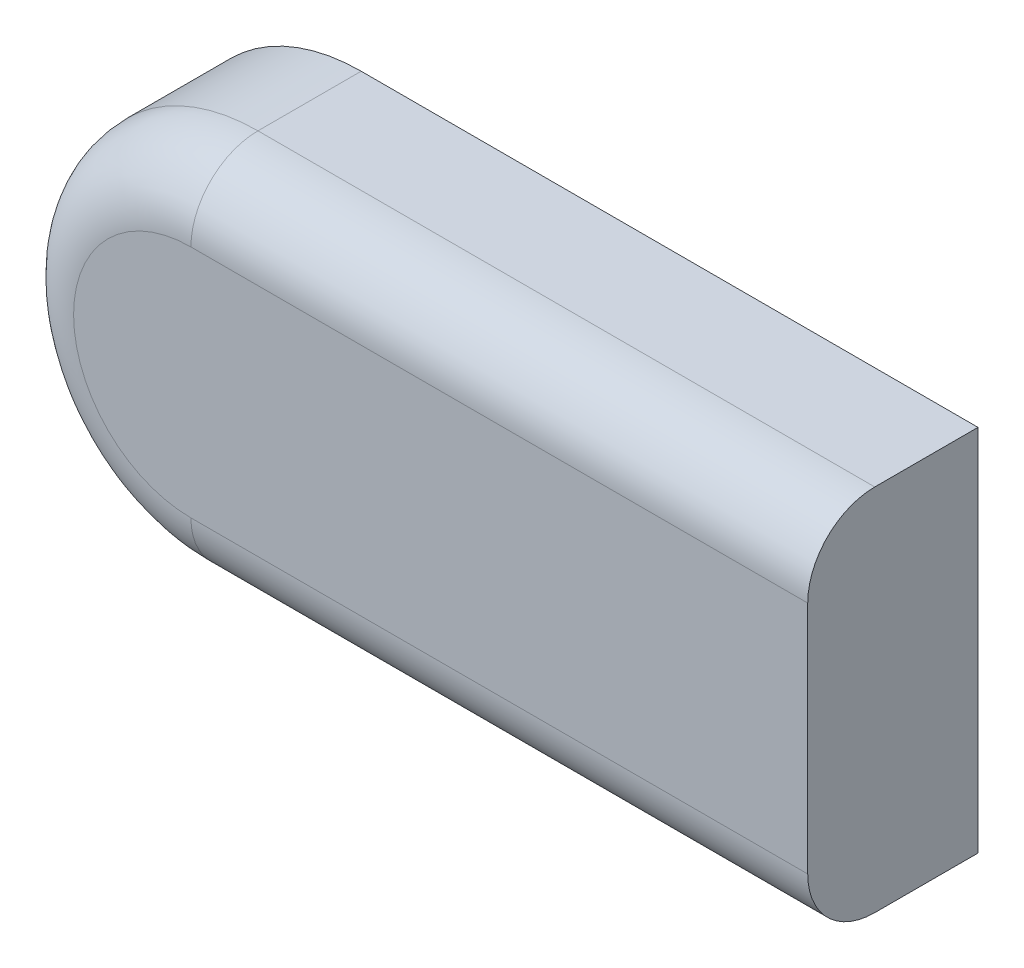
SolidWorks part; units mm, degrees
ref_plane "Front Plane" through (0, 0, 0) normal (0, 0, 1) x (1, 0, 0)
ref_plane "Top Plane" through (0, 0, 0) normal (0, 1, 0) x (1, 0, 0)
ref_plane "Right Plane" through (0, 0, 0) normal (1, 0, 0) x (0, 0, -1)
sketch "Sketch4" plane through (0, 0, 0) normal (0, 0, 1) x (1, 0, 0)
  line L1 (79.1182, 41.2761) -> (-12.8937, 41.2761)
  line L2 (79.1182, 41.2761) -> (79.1182, -13.7239)
  line L3 (79.1182, -13.7239) -> (-12.8937, -13.7239)
  line L5 (-12.4727, 38.2761) -> (76.1182, 38.2761)
  line L7 (-12.4727, -10.7239) -> (76.1182, -10.7239)
  line L8 (76.1182, 38.2761) -> (76.1182, -10.7239)
  arc A0 (-12.8937, 41.2761) -> (-12.8937, -13.7239) centre (-12.8937, 13.7761) ccw
  arc A1 (-12.4727, 38.2761) -> (-12.4727, -10.7239) centre (-12.4727, 13.7761) ccw
  point P6 (0, 0)
  point P11 (0, 0)
  point P12 (-10.3172, 13.7761)
  dimension "D1" = 27.5
  dimension "D2" = 92.0119
  dimension "D3" = 55
  dimension "D4" = 92.0119
  dimension "D5" = 3
  dimension "D6" = 3
  dimension "D7" = 3
extrude "Boss-Extrude3" add sketch "Sketch4" along normal blind 25.4
sketch "Sketch6" plane through (0, 0, 25.4) normal (0, 0, 1) x (1, 0, 0)
  line L1 (-12.8937, 41.2761) -> (79.1182, 41.2761)
  line L3 (-12.8937, -13.7239) -> (79.1182, -13.7239)
  line L4 (79.1182, 41.2761) -> (79.1182, -13.7239)
  arc A0 (-12.8937, 41.2761) -> (-12.8937, -13.7239) centre (-12.8937, 13.7761) ccw
extrude "Boss-Extrude4" add sketch "Sketch6" against normal blind 4
fillet "Fillet2" radius 10 3 edges at (33.1123, -13.7239, 25.4) (-40.3937, 13.7761, 25.4) (33.1123, 41.2761, 25.4)
